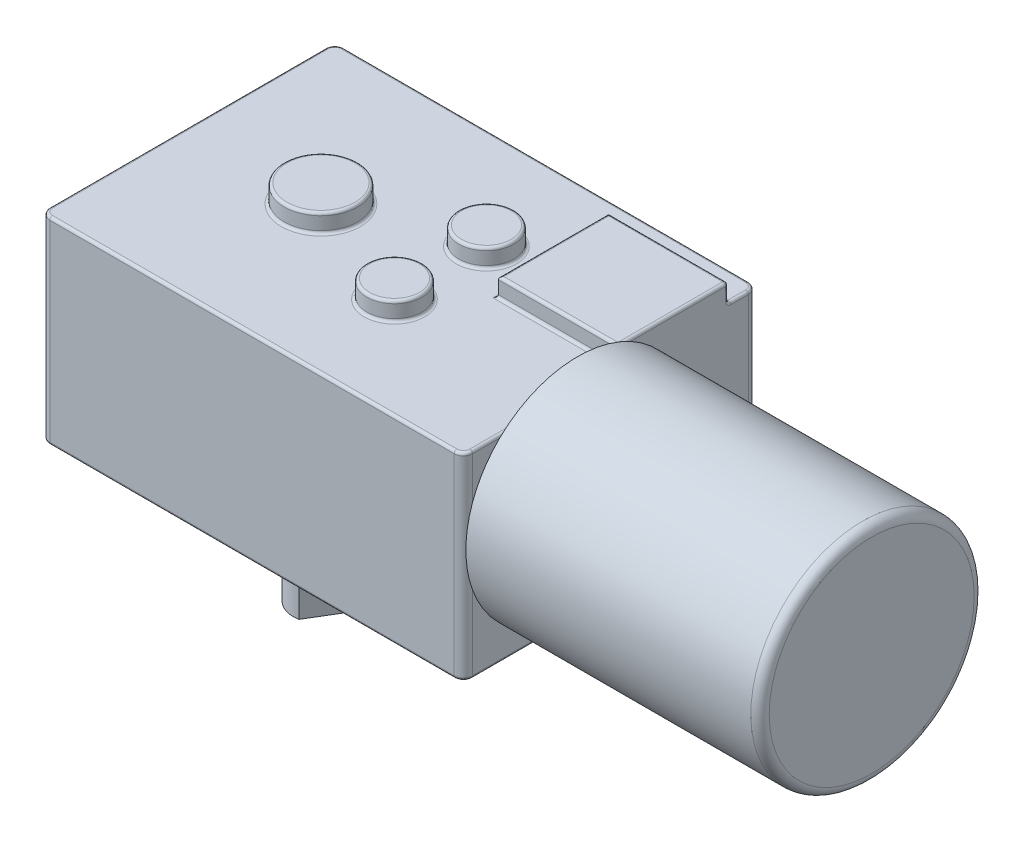
SolidWorks part; units mm, degrees
ref_plane "Front Plane" through (0, 0, 0) normal (0, 0, 1) x (1, 0, 0)
ref_plane "Top Plane" through (0, 0, 0) normal (0, 1, 0) x (1, 0, 0)
ref_plane "Right Plane" through (0, 0, 0) normal (1, 0, 0) x (0, 0, -1)
sketch "Sketch1" plane through (0, 0, 0) normal (0, 1, 0) x (1, 0, 0)
  line L1 (-23, 16) -> (23, 16)
  line L2 (-23, 16) -> (-23, -16)
  line L3 (-23, -16) -> (23, -16)
  line L4 (23, 16) -> (23, -16)
  line L5 (-23, 16) -> (23, -16) construction
  line L6 (-23, -16) -> (23, 16) construction
  point P0 (0, 0)
  dimension "D1" = 32
  dimension "D2" = 46
extrude "Boss-Extrude1" add sketch "Sketch1" along normal blind 21.5
fillet "Fillet1" radius 1 4 edges at (-23, 10.75, -16) (-23, 10.75, 16) (23, 10.75, -16) (23, 10.75, 16)
sketch "Sketch2" plane through (0, 21.5, 0) normal (0, 1, 0) x (1, 0, 0)
  line L0 (23, -15) -> (23, 15) construction
  line L1 (23, 12.8) -> (10, 12.8)
  line L2 (23, 12.8) -> (23, 0.8)
  line L3 (23, 0.8) -> (10, 0.8)
  line L4 (10, 12.8) -> (10, 0.8)
  line L5 (22, 16) -> (-22, 16) construction
  dimension "D1" = 3.2
  dimension "D2" = 12
  dimension "D3" = 13
extrude "Boss-Extrude2" add sketch "Sketch2" along normal blind 2
sketch "Sketch3" plane through (0, 21.5, 0) normal (0, 1, 0) x (1, 0, 0)
  line L0 (-23, 0) -> (-8.5, 0) construction
  line L1 (-23, 15) -> (-23, -15) construction
  line L3 (-8.5, 0) -> (4.5, 0) construction
  line L4 (4.5, 0) -> (4.5, 5) construction
  line L5 (4.5, 0) -> (4.5, -5) construction
  circle A0 centre (-8.5, 0) radius 4
  circle A1 centre (4.5, 5) radius 3
  circle A2 centre (4.5, -5) radius 3
  dimension "D2" = 8
  dimension "D3" = 6
  dimension "D4" = 6
  dimension "D1" = 14.5
  dimension "D5" = 13
  dimension "D6" = 5
  dimension "D7" = 5
extrude "Boss-Extrude3" add sketch "Sketch3" along normal blind 2
sketch "Sketch4" plane through (0, 0, 0) normal (0, -1, 0) x (1, 0, 0)
  line L0 (-23, 0) -> (-8.5, 0) construction
  line L1 (-23, -15) -> (-23, 15) construction
  line L2 (-16.4, 9.4) -> (16.4, 9.4) construction
  line L3 (16.4, 9.4) -> (16.4, -9.4) construction
  line L4 (16.4, -9.4) -> (-16.4, -9.4) construction
  line L5 (-16.4, -9.4) -> (-16.4, 9.4) construction
  line L6 (-22, 16) -> (22, 16) construction
  line L7 (23, 15) -> (23, -15) construction
  line L8 (22, -16) -> (-22, -16) construction
  circle A0 centre (-8.5, 0) radius 6.75
  circle A1 centre (-16.4, 9.4) radius 4
  circle A2 centre (-16.4, 9.4) radius 1.5
  circle A3 centre (-16.4, -9.4) radius 4
  circle A4 centre (-16.4, -9.4) radius 1.5
  circle A6 centre (16.4, -9.4) radius 1.5
  circle A7 centre (16.4, -9.4) radius 4
  circle A8 centre (16.4, 9.4) radius 1.5
  circle A9 centre (16.4, 9.4) radius 4
  circle A10 centre (4.5, 5) radius 3
  circle A11 centre (4.5, -5) radius 3
  dimension "D2" = 13.5
  dimension "D7" = 3
  dimension "D8" = 8
  dimension "D9" = 8
  dimension "D10" = 3
  dimension "D11" = 3
  dimension "D12" = 8
  dimension "D13" = 3
  dimension "D14" = 8
  dimension "D1" = 14.5
  dimension "D3" = 6.6
  dimension "D4" = 6.6
  dimension "D5" = 6.6
  dimension "D6" = 6.6
extrude "Boss-Extrude4" add sketch "Sketch4" along normal blind 2
fillet "Fillet2" radius 0.3 49 edges at (23, 22.5, -0.8) (23, 22.5, -12.8) (4.5, 23.5, 8) (16.5, 23.5, -0.8) (10, 23.5, -6.8) (16.5, 23.5, -12.8) (23, 23.5, -6.8) (4.5, 23.5, -2) (-8.5, 23.5, 4) (-16.4, -2, -10.9) (-16.4, -2, -13.4) (16.4, -2, -10.9) (16.4, -2, -13.4) (16.4, -2, 7.9) (16.4, -2, 5.4) (4.5, -2, -8) (4.5, -2, 2) (-16.4, -2, 7.9) (-16.4, -2, 5.4) (-22.7071, 0, 15.7071) (0, 0, 16) (22.7071, 0, 15.7071) (23, 0, 0) (22.7071, 0, -15.7071) (0, 0, -16) (-22.7071, 0, -15.7071) (-23, 0, 0) (-8.5, 0, -6.75) (-16.4, 0, 13.4) (-16.4, 0, -5.4) (16.4, 0, -5.4) (16.4, 0, 13.4) (4.5, 0, 8) (4.5, 0, -2) (23, 21.5, 7.1) (22.7071, 21.5, 15.7071) (0, 21.5, 16) (-22.7071, 21.5, 15.7071) (-23, 21.5, 0) (-22.7071, 21.5, -15.7071) (0, 21.5, -16) (22.7071, 21.5, -15.7071) (23, 21.5, -13.9) (16.5, 21.5, -12.8) (10, 21.5, -6.8) (16.5, 21.5, -0.8) (-8.5, 21.5, 4) (4.5, 21.5, -2) (4.5, 21.5, 8)
sketch "Sketch5" plane through (23, 0, 0) normal (1, 0, 0) x (0, 0, -1)
  line L0 (-3.584, 12.5) -> (0, 12.5) construction
  line L1 (0, 12.5) -> (0, 0) construction
  circle A0 centre (-3.584, 12.5) radius 12.15
  dimension "D1" = 24.3
  dimension "D2" = 12.5
extrude "Boss-Extrude5" add sketch "Sketch5" along normal blind 32
fillet "Fillet3" radius 1 1 edges at (55, 12.5, -8.566)
sketch "Sketch6" plane through (0, -2, 0) normal (0, 1, 0) x (1, 0, 0)
  circle A0 centre (-8.5, 0) radius 5
  dimension "D1" = 10
extrude "Cut-Extrude1" cut sketch "Sketch6" along normal blind 0.1
sketch "Sketch7" plane through (0, -1.9, 0) normal (0, -1, 0) x (1, 0, 0)
  circle A1 centre (-8.5, 0) radius 3
extrude "Boss-Extrude6" add sketch "Sketch7" along normal blind 14
sketch "Sketch8" plane through (0, -15.9, 0) normal (0, -1, 0) x (1, 0, 0)
  line L0 (-7.9392, 2.9471) -> (-5.6334, -0.8848)
  line L1 (-7.9392, 2.9471) -> (-4.6301, 4.9384)
  line L2 (-5.6334, -0.8848) -> (-2.3243, 1.1065)
  line L3 (-4.6301, 4.9384) -> (-2.3243, 1.1065)
  circle A0 centre (-8.5, 0) radius 3 construction
  circle A1 centre (-8.5, 0) radius 3 construction
  dimension "D1" = 2
extrude "Cut-Extrude2" cut sketch "Sketch8" against normal blind 11
